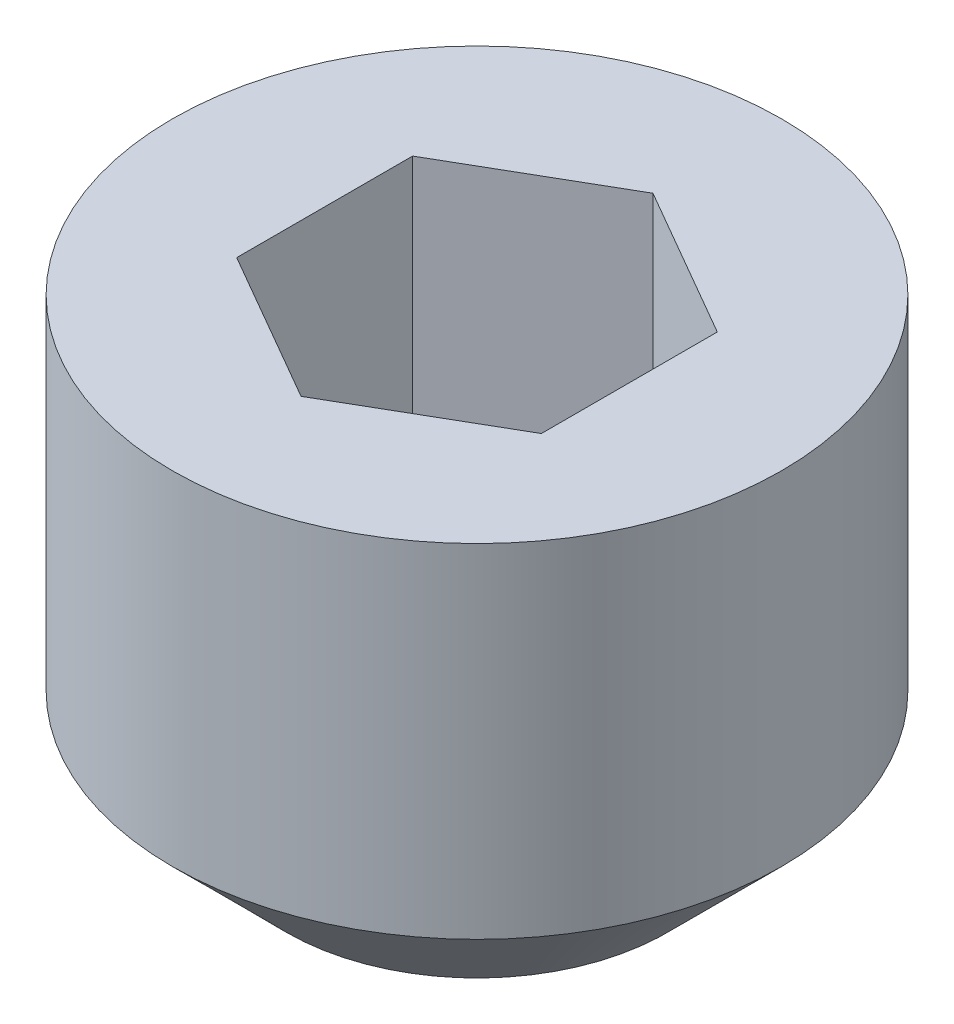
SolidWorks part; units mm, degrees
ref_plane "Front Plane" through (0, 0, 0) normal (0, 0, 1) x (1, 0, 0)
ref_plane "Top Plane" through (0, 0, 0) normal (0, 1, 0) x (1, 0, 0)
ref_plane "Right Plane" through (0, 0, 0) normal (1, 0, 0) x (0, 0, -1)
sketch "Sketch1" plane through (0, 0, 0) normal (0, 0, 1) x (1, 0, 0)
  line L0 (0, 3) -> (0, 0) construction
  line L1 (0, 3) -> (2, 3)
  line L2 (2, 3) -> (2, 0)
  line L3 (2, 0) -> (0, 0)
  line L4 (0, 3) -> (0, 0)
  dimension "SS_M" = 4
  dimension "SS_L" = 3
revolve "Revolve1" add sketch "Sketch1" angle 360 about L0
cosmetic thread "Cosmetic Thread1" parameters "SS_D1_s"=3.242
sketch "Sketch2" plane through (0, 0, 0) normal (0, 0, 1) x (1, 0, 0)
  line L0 (0, 3) -> (0, 0.9226) construction
  line L1 (0, 3) -> (1, 3)
  line L2 (1, 3) -> (1, 1.5)
  line L3 (1, 1.5) -> (0, 0.9226)
  line L4 (0, 3) -> (0, 0.9226)
  line L5 (2, 3) -> (-2, 3) construction
  dimension "D3" = 60
  dimension "SS_C" = 1.5
  dimension "SS_B" = 2
revolve "Cut-Revolve1" cut sketch "Sketch2" angle 360 about L0
sketch "Sketch3" plane through (0, 3, 0) normal (0, 1, 0) x (1, 0, 0)
  line L1 (0, 1.1547) -> (-1, 0.5774)
  line L2 (-1, 0.5774) -> (-1, -0.5774)
  line L3 (-1, -0.5774) -> (0, -1.1547)
  line L4 (0, -1.1547) -> (1, -0.5774)
  line L5 (1, -0.5774) -> (1, 0.5774)
  line L6 (1, 0.5774) -> (0, 1.1547)
  circle A0 centre (0, 0) radius 1 construction
  circle A1 centre (0, 0) radius 1 construction
extrude "Cut-Extrude1" cut sketch "Sketch3" against normal blind 1.5
sketch "Sketch4" plane through (0, 0, 0) normal (0, 0, 1) x (1, 0, 0)
  line L0 (1.25, 0) -> (2, 0)
  line L1 (2, 0) -> (2, 0.75)
  line L2 (2, 0.75) -> (1.25, 0)
  line L4 (-2, 0) -> (2, 0) construction
  line L5 (0, 0) -> (0, 3) construction
  line L6 (2, 3) -> (-2, 3) construction
  line L7 (2, 3) -> (2, 0) construction
  dimension "D1" = 45
  dimension "SS_D_s" = 2.5
revolve "Cut-Revolve2" cut sketch "Sketch4" angle 360 about L5
